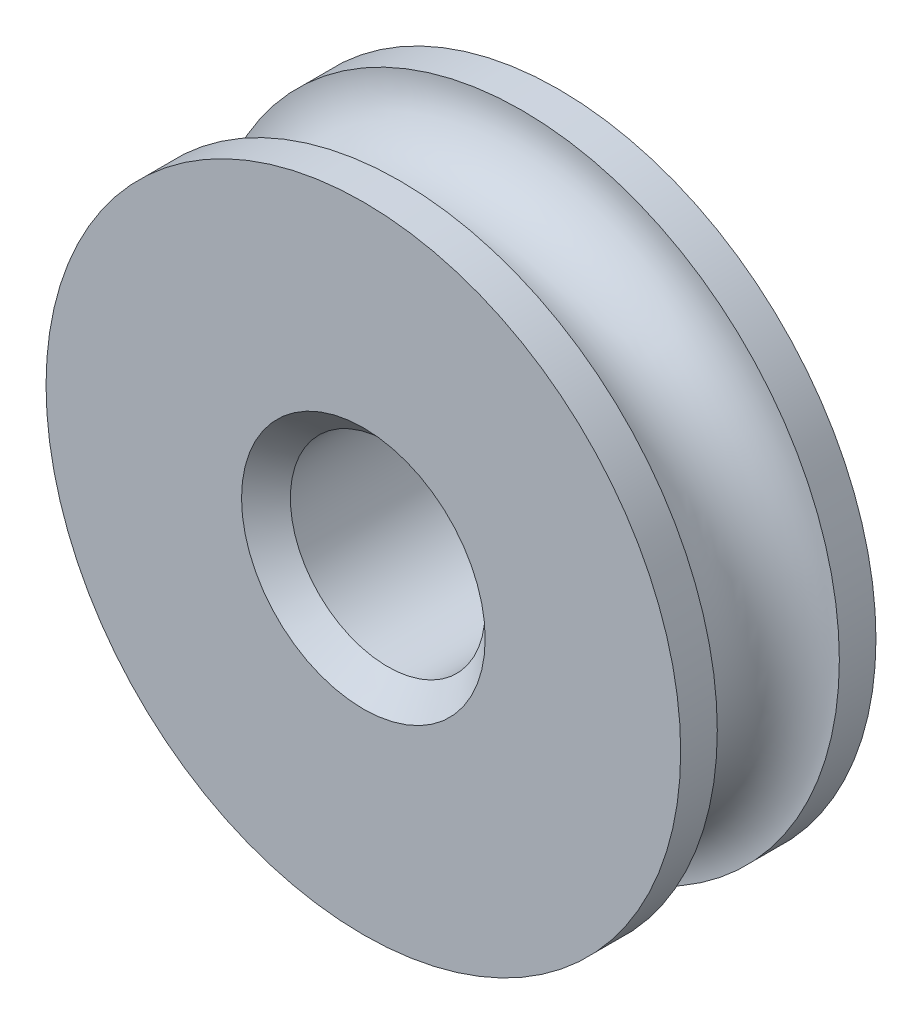
SolidWorks part; units mm, degrees
ref_plane "Alzado" through (0, 0, 0) normal (0, 0, 1) x (1, 0, 0)
ref_plane "Planta" through (0, 0, 0) normal (0, 1, 0) x (1, 0, 0)
ref_plane "Vista lateral" through (0, 0, 0) normal (1, 0, 0) x (0, 0, -1)
ref_plane "Plano1" through (0, -190, 0) normal (0, 1, 0) x (1, 0, 0)
sketch "Croquis1" plane through (0, -190, 0) normal (0, 1, 0) x (1, 0, 0)
  line L0 (-55, 0) -> (55, 0) construction
  line L1 (6.5, 0) -> (6.5, 0.75)
  line L2 (0, -55) -> (0, 55) construction
  line L3 (6.5, 4) -> (1.9956, 4)
  line L4 (1.9956, 4) -> (1.9956, 0)
  line L5 (1.9956, 0) -> (6.5, 0)
  line L6 (0, 5) -> (0, 0) construction
  line L7 (6.5, 3.25) -> (6.5, 4)
  arc A0 (6.5, 3.25) -> (6.5, 0.75) centre (6.5, 2) ccw
  dimension "D4" = 2.5
  dimension "D1" = 4
  dimension "D2" = 6.5
  dimension "D3" = 1.9956
  dimension "D5" = 2
revolve "Revolución1" add sketch "Croquis1" angle 360 about L6
chamfer "Chaflán2" distance 0.5 angle 45 2 edges at (1.9956, -190, 0) (1.9956, -190, -4)
